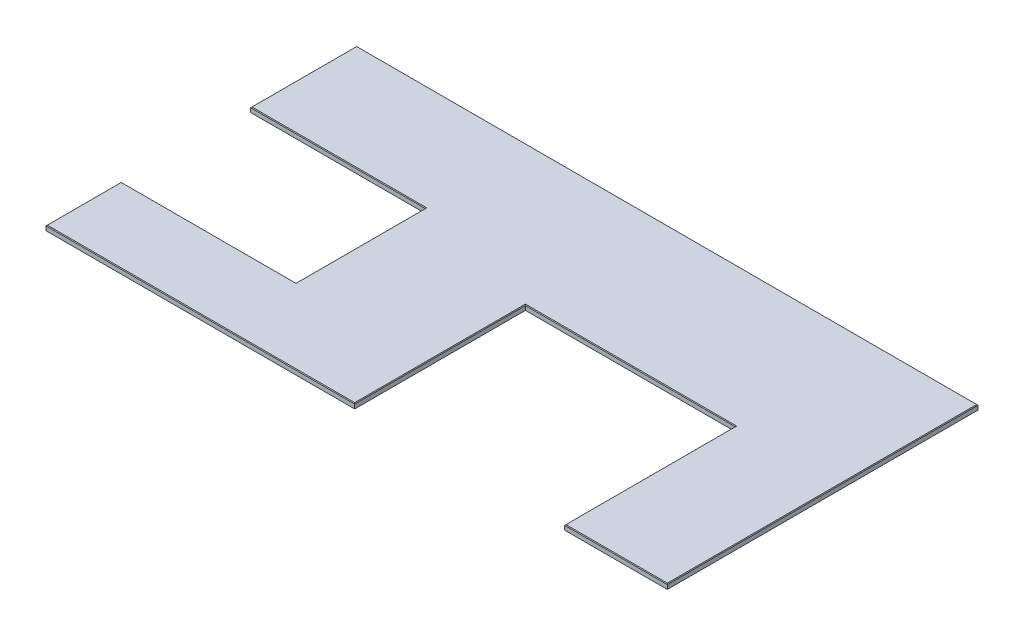
SolidWorks part; units mm, degrees
material "Oak"
ref_plane "Front Plane" through (0, 0, 0) normal (0, 0, 1) x (1, 0, 0)
ref_plane "Top Plane" through (0, 0, 0) normal (0, 1, 0) x (1, 0, 0)
ref_plane "Right Plane" through (0, 0, 0) normal (1, 0, 0) x (0, 0, -1)
sketch "Sketch1" plane through (0, 0, 0) normal (0, 1, 0) x (1, 0, 0)
  line L0 (1211.5165, 0) -> (1211.5165, 669.925)
  line L1 (1211.5165, 669.925) -> (2035.429, 669.925)
  line L2 (2035.429, 669.925) -> (2035.429, 0)
  line L3 (2035.429, 0) -> (2438.4, 0)
  line L4 (2438.4, 0) -> (2438.4, 1219.2)
  line L5 (2438.4, 1219.2) -> (0, 1219.2)
  line L6 (0, 1219.2) -> (0, 803.275)
  line L7 (0, 0) -> (1211.5165, 0)
  line L8 (0, 295.275) -> (0, 0)
  line L9 (0, 803.275) -> (685.8, 803.275)
  line L11 (0, 295.275) -> (685.8, 295.275)
  line L12 (685.8, 803.275) -> (685.8, 295.275)
  dimension "D1" = 2438.4
  dimension "D2" = 1211.5165
  dimension "D3" = 823.9125
  dimension "D4" = 669.925
  dimension "D5" = 1219.2
  dimension "D6" = 685.8
  dimension "D7" = 295.275
  dimension "D8" = 415.925
extrude "Boss-Extrude1" add sketch "Sketch1" against normal blind 19.05
chamfer "Chamfer1" distance 2.54 angle 45 12 edges at (0, 0, -1011.2375) (1219.2, 0, -1219.2) (2438.4, 0, -609.6) (2236.9145, 0, 0) (2035.429, 0, -334.9625) (1623.4727, 0, -669.925) (1211.5165, 0, -334.9625) (605.7583, 0, 0) (0, 0, -147.6375) (342.9, 0, -295.275) (685.8, 0, -549.275) (342.9, 0, -803.275)
